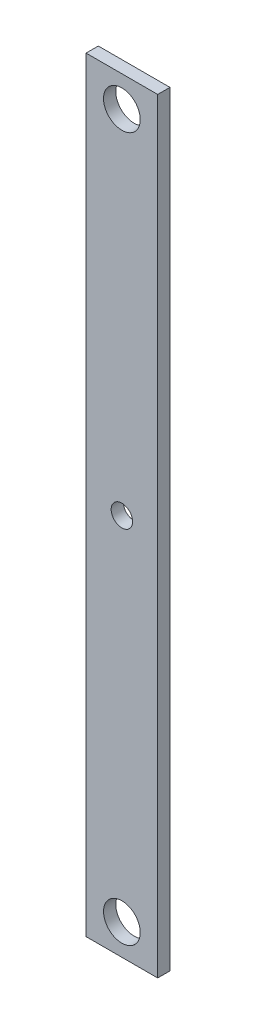
SolidWorks part; units mm, degrees
material "Alloy Steel"
ref_plane "Front Plane" through (0, 0, 0) normal (0, 0, 1) x (1, 0, 0)
ref_plane "Top Plane" through (0, 0, 0) normal (0, 1, 0) x (1, 0, 0)
ref_plane "Right Plane" through (0, 0, 0) normal (1, 0, 0) x (0, 0, -1)
sketch "Sketch1" plane through (0, 0, 0) normal (0, 0, 1) x (1, 0, 0)
  line L1 (-5.85, -62.5) -> (5.85, -62.5)
  line L2 (-5.85, -62.5) -> (-5.85, 62.5)
  line L3 (-5.85, 62.5) -> (5.85, 62.5)
  line L4 (5.85, -62.5) -> (5.85, 62.5)
  line L5 (-5.85, -62.5) -> (5.85, 62.5) construction
  line L6 (-5.85, 62.5) -> (5.85, -62.5) construction
  point P0 (0, 0)
  dimension "D1" = 11.7
  dimension "D2" = 125
extrude "Boss-Extrude1" add sketch "Sketch1" along normal mid plane 2
sketch "Sketch2" plane through (0, 0, 1) normal (0, 0, 1) x (1, 0, 0)
  line L0 (5.85, 62.5) -> (-5.85, 62.5) construction
  line L1 (-5.85, -62.5) -> (5.85, -62.5) construction
  circle A0 centre (0, 57.5) radius 3
  circle A1 centre (0, -57.5) radius 3
  dimension "D3" = 6
  dimension "D4" = 6
  dimension "D1" = 5
  dimension "D2" = 5
extrude "Cut-Extrude1" cut sketch "Sketch2" against normal through all
sketch "Sketch3" plane through (0, 0, 1) normal (0, 0, 1) x (1, 0, 0)
  circle A0 centre (0, 0) radius 1.75
  dimension "D1" = 3.5
extrude "Cut-Extrude2" cut sketch "Sketch3" against normal blind 10
equation "\"Largeur\"= 11.7"
equation "\"Longueur\"= 125"
equation "\"Epaisseur\"= 2"
equation "\"D2@Sketch1\"=\"Longueur\""
equation "\"D1@Sketch1\"=\"Largeur\""
equation "\"D1@Boss-Extrude1\"=\"Epaisseur\""
equation "\"LargeurPlaqueEpaisse\"= 10mm"
equation "\"D1@Sketch2\"=\"LargeurPlaqueEpaisse\"/2"
equation "\"D2@Sketch2\"=\"LargeurPlaqueEpaisse\"/2"
equation "\"DiametreTrou\"= 6mm"
equation "\"D3@Sketch2\"=\"DiametreTrou\""
equation "\"D4@Sketch2\"=\"DiametreTrou\""
